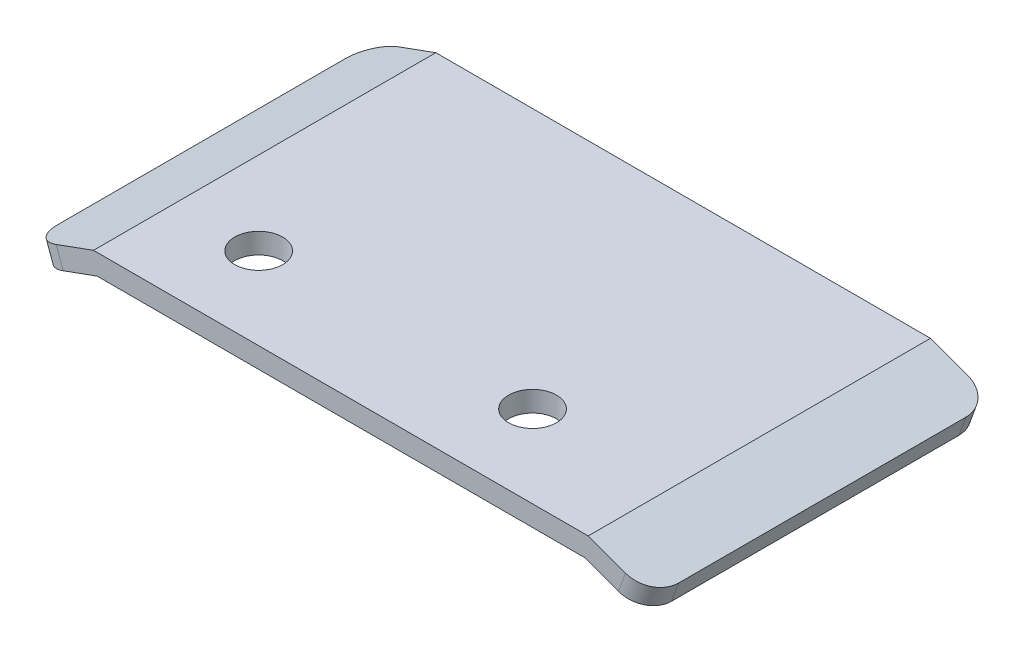
SolidWorks part; units mm, degrees
ref_plane "Front Plane" through (0, 0, 0) normal (0, 0, 1) x (1, 0, 0)
ref_plane "Top Plane" through (0, 0, 0) normal (0, 1, 0) x (1, 0, 0)
ref_plane "Right Plane" through (0, 0, 0) normal (1, 0, 0) x (0, 0, -1)
sketch "Sketch1" plane through (0, 0, 0) normal (0, 0, 1) x (1, 0, 0)
  line L0 (-19.6016, 4.273) -> (-14.9971, 5.9489)
  line L1 (-14.9971, 5.9489) -> (21.1319, 5.9489)
  line L2 (21.1319, 5.9489) -> (25.7364, 4.273)
  line L3 (-19.0886, 2.8634) -> (-14.7326, 4.4489)
  line L4 (-14.7326, 4.4489) -> (20.8674, 4.4489)
  line L5 (20.8674, 4.4489) -> (25.2233, 2.8634)
  line L6 (-19.6016, 4.273) -> (-19.0886, 2.8634)
  line L7 (25.7364, 4.273) -> (25.2233, 2.8634)
  dimension "D1" = 35.6
  dimension "D2" = 20
  dimension "D3" = 20
  dimension "D4" = 4.9
  dimension "D5" = 4.9
  dimension "D6" = 1.5
extrude "Boss-Extrude1" add sketch "Sketch1" along normal blind 25
sketch "Sketch2" plane through (0, 4.4489, 0) normal (0, -1, 0) x (1, 0, 0)
  line L0 (-14.7326, 25) -> (-14.7326, 0) construction
  line L1 (-14.7326, 25) -> (20.8674, 25) construction
  circle A0 centre (-8.9326, 19) radius 1.75
  circle A1 centre (11.0674, 19) radius 1.75
  dimension "D1" = 3.5
  dimension "D2" = 20
  dimension "D4" = 6
  dimension "D3" = 5.8
extrude "Cut-Extrude1" cut sketch "Sketch2" against normal through all
fillet "Fillet1" radius 2 4 edges at (25.4799, 3.5682, 25) (25.4799, 3.5682, 0) (-19.3451, 3.5682, 0) (-19.3451, 3.5682, 25)
